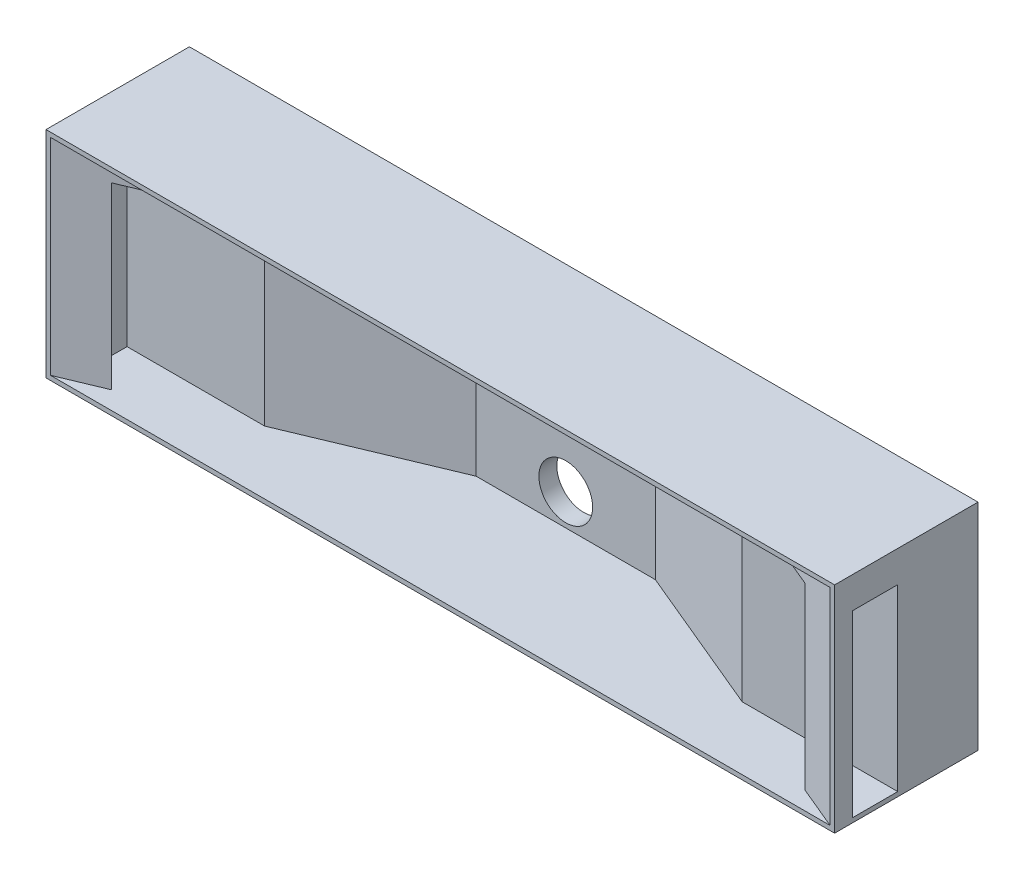
SolidWorks part; units mm, degrees
ref_plane "Front Plane" through (0, 0, 0) normal (0, 0, 1) x (1, 0, 0)
ref_plane "Top Plane" through (0, 0, 0) normal (0, 1, 0) x (1, 0, 0)
ref_plane "Right Plane" through (0, 0, 0) normal (1, 0, 0) x (0, 0, -1)
sketch "Sketch1" plane through (0, 0, 0) normal (0, 0, 1) x (1, 0, 0)
  line L1 (0, 0) -> (558.8, 0)
  line L2 (0, 0) -> (0, 152.4)
  line L3 (0, 152.4) -> (558.8, 152.4)
  line L4 (558.8, 0) -> (558.8, 152.4)
  line L5 (3.175, 3.175) -> (555.625, 3.175)
  line L6 (3.175, 3.175) -> (3.175, 149.225)
  line L7 (3.175, 149.225) -> (555.625, 149.225)
  line L8 (555.625, 3.175) -> (555.625, 149.225)
  dimension "D1" = 152.4
  dimension "D2" = 558.8
  dimension "D3" = 3.175
  dimension "D4" = 3.175
  dimension "D5" = 3.175
  dimension "D6" = 3.175
extrude "Boss-Extrude2" add sketch "Sketch1" along normal blind 101.6
sketch "Sketch2" plane through (0, 3.175, 0) normal (0, 1, 0) x (1, 0, 0)
  line L0 (3.175, -101.6) -> (215.9, -12.7)
  line L1 (558.8, 0) -> (0, 0) construction
  line L3 (342.9, -12.7) -> (555.625, -101.6)
  line L4 (555.625, -101.6) -> (555.625, -12.7)
  line L5 (555.625, -12.7) -> (342.9, -12.7)
  line L6 (3.175, -101.6) -> (3.175, -12.7)
  line L7 (3.175, -12.7) -> (215.9, -12.7)
  dimension "D1" = 12.7
  dimension "D2" = 127
extrude "Boss-Extrude3" add sketch "Sketch2" along normal up to next
sketch "Sketch5" plane through (0, 0, 12.7) normal (0, 0, -1) x (-1, 0, 0)
  line L1 (-555.625, 149.225) -> (-3.175, 149.225) construction
  line L2 (-3.175, 3.175) -> (-555.625, 3.175) construction
  line L4 (-555.625, 149.225) -> (-3.175, 149.225)
  line L5 (-555.625, 149.225) -> (-555.625, 3.175)
  line L6 (-555.625, 3.175) -> (-3.175, 3.175)
  line L7 (-3.175, 149.225) -> (-3.175, 3.175)
  circle A0 centre (-279.4, 19.05) radius 15.875
  point P8 (-279.4, 149.225)
  dimension "D1" = 31.75
extrude "Boss-Extrude15" add sketch "Sketch5" along normal blind 12.7 contours L6 A0 L4 L5 | L5 L1 L2 L4 | A0
sketch "Sketch8" plane through (0, 0, 0) normal (0, 0, -1) x (-1, 0, 0)
  line L1 (0, 0) -> (-558.8, 0) construction
  circle A0 centre (-279.4, 25.4) radius 19.05
  dimension "D1" = 38.1
  dimension "D2" = 25.4
extrude "Cut-Extrude1" cut sketch "Sketch8" against normal through all
sketch "Sketch9" plane through (558.8, 0, 0) normal (1, 0, 0) x (0, 0, -1)
  line L0 (-101.6, 0) -> (-101.6, 152.4) construction
  line L1 (-88.9, 130.175) -> (-56.8648, 130.175)
  line L2 (-88.9, 130.175) -> (-88.9, 3.175)
  line L3 (-88.9, 3.175) -> (-56.8648, 3.175)
  line L4 (-56.8648, 130.175) -> (-56.8648, 3.175)
  line L5 (-101.6, 0) -> (0, 0) construction
  dimension "D1" = 12.7
  dimension "D2" = 3.175
  dimension "D3" = 127
extrude "Cut-Extrude2" cut sketch "Sketch9" against normal blind 546.1
